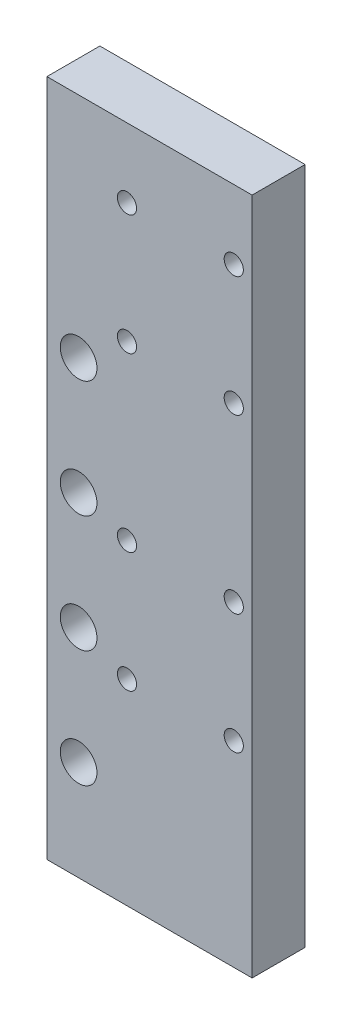
SolidWorks part; units mm, degrees
ref_plane "Front Plane" through (0, 0, 0) normal (0, 0, 1) x (1, 0, 0)
ref_plane "Top Plane" through (0, 0, 0) normal (0, 1, 0) x (1, 0, 0)
ref_plane "Right Plane" through (0, 0, 0) normal (1, 0, 0) x (0, 0, -1)
sketch "Sketch1" plane through (0, 0, 0) normal (0, 0, 1) x (1, 0, 0)
  line L1 (-30.75, 101.6) -> (30.75, 101.6)
  line L2 (-30.75, 101.6) -> (-30.75, -101.6)
  line L3 (-30.75, -101.6) -> (30.75, -101.6)
  line L4 (30.75, 101.6) -> (30.75, -101.6)
  line L5 (-30.75, 101.6) -> (30.75, -101.6) construction
  line L6 (-30.75, -101.6) -> (30.75, 101.6) construction
  point P0 (0, 0)
  dimension "D1" = 203.2
  dimension "D2" = 61.5
extrude "Boss-Extrude1" add sketch "Sketch1" along normal mid plane 15.875
sketch "Sketch2" plane through (0, 0, 7.9375) normal (0, 0, 1) x (1, 0, 0)
  line L0 (-21.25, 101.6) -> (-21.25, -101.6) construction
  line L1 (30.75, 101.6) -> (-30.75, 101.6) construction
  line L2 (-30.75, -101.6) -> (30.75, -101.6) construction
  line L3 (-30.75, 101.6) -> (-30.75, -101.6) construction
  circle A0 centre (-21.25, 33.4) radius 5.5
  circle A1 centre (-21.25, -1.6) radius 5.5
  circle A2 centre (-21.25, -36.6) radius 5.5
  circle A3 centre (-21.25, -71.6) radius 5.5
  dimension "D2" = 11
  dimension "D1" = 9.5
  dimension "D3" = 30
  dimension "D4" = 35
  dimension "D5" = 35
  dimension "D6" = 35
extrude "Cut-Extrude1" cut sketch "Sketch2" against normal through all
sketch "Sketch3" plane through (0, 0, 7.9375) normal (0, 0, 1) x (1, 0, 0)
  line L0 (-6.75, 101.6) -> (-6.75, -101.6) construction
  line L1 (30.75, 101.6) -> (-30.75, 101.6) construction
  line L2 (-30.75, -101.6) -> (30.75, -101.6) construction
  line L3 (-30.75, 101.6) -> (-30.75, -101.6) construction
  circle A0 centre (-6.75, 80.85) radius 2.875
  circle A1 centre (-6.75, 44.85) radius 2.875
  circle A2 centre (-6.75, -6.75) radius 2.875
  circle A3 centre (-6.75, -42.75) radius 2.875
  dimension "D2" = 5.75
  dimension "D1" = 24
  dimension "D3" = 20.75
  dimension "D4" = 36
  dimension "D5" = 51.6
  dimension "D6" = 36
extrude "Cut-Extrude2" cut sketch "Sketch3" against normal through all
pattern_linear "LPattern1" count 2 spacing 32 along (1, 0, 0) of "Cut-Extrude2"
